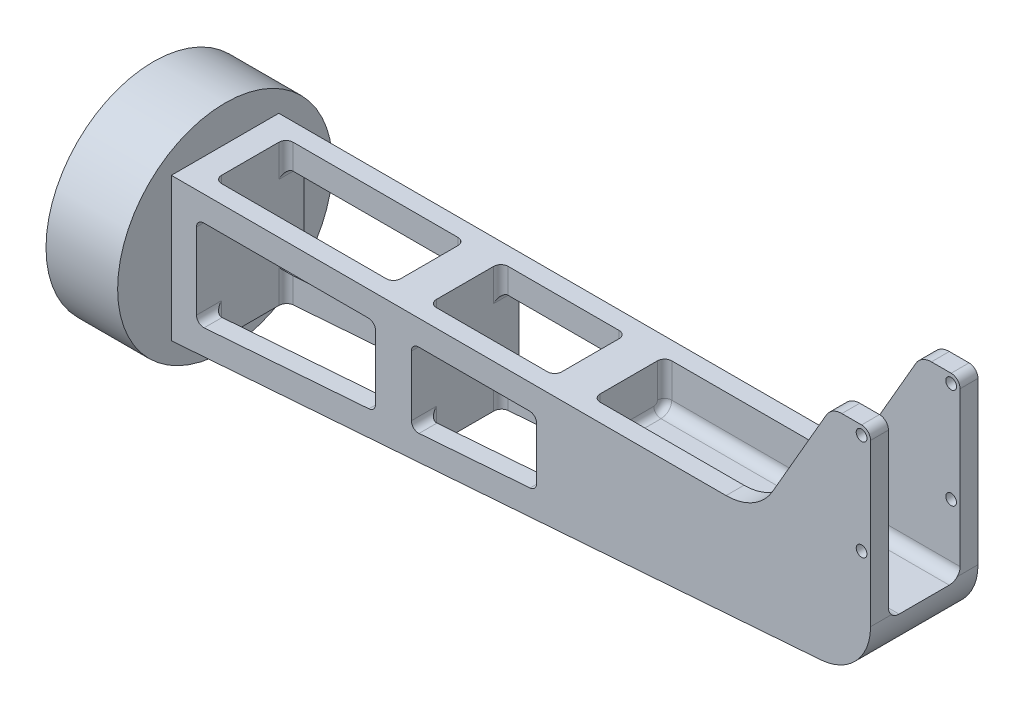
SolidWorks part; units mm, degrees
ref_plane "Front Plane" through (0, 0, 0) normal (0, 0, 1) x (1, 0, 0)
ref_plane "Top Plane" through (0, 0, 0) normal (0, 1, 0) x (1, 0, 0)
ref_plane "Right Plane" through (0, 0, 0) normal (1, 0, 0) x (0, 0, -1)
sketch "SideProfile" plane through (0, 0, 0) normal (0, 0, 1) x (1, 0, 0)
  line L0 (0, 0) -> (0, 28) construction
  line L1 (0, 28) -> (78.5, 28) construction
  line L2 (78.5, 28) -> (72.0655, 14.4502) construction
  line L3 (72.0655, 14.4502) -> (0, 0) construction
  line L4 (0, 0) -> (-27.9563, 16.574) construction
  line L5 (-27.9563, 16.574) -> (-60.4805, -10) construction
  line L6 (72.0655, 14.4502) -> (145.1629, -45.4258) construction
  line L7 (145.1629, -45.4258) -> (122.4038, 18.425) construction
  line L8 (75.2828, 21.2251) -> (98.855, 10.0312) construction
  line L9 (98.855, 10.0312) -> (122.4038, 18.425) construction
  line L10 (-192.7, -25.5) -> (0, -25.5) construction
  line L11 (-192.7, -25.5) -> (-192.7, -81.51) construction
  line L12 (-60.48, -18) -> (0, -18) construction
  line L14 (-212.7, 4.5) -> (-192.7, 4.5) construction
  line L15 (-212.7, 4.5) -> (-212.7, -55.5) construction
  line L16 (-212.7, -55.5) -> (-192.7, -55.5) construction
  line L17 (-192.7, 4.5) -> (-192.7, -55.5) construction
  circle A0 centre (0, 28) radius 2.5 construction
  circle A1 centre (0, 28) radius 1.5 construction
  point P22 (-192.7, -25.5)
  dimension "D18" = 5
  dimension "D19" = 3
  dimension "D1" = 28
  dimension "D2" = 78.5
  dimension "D3" = 15
  dimension "D4" = 73.5
  dimension "D5" = 138
  dimension "D6" = 32.5
  dimension "D7" = 42
  dimension "D8" = 10
  dimension "D9" = 94.49
  dimension "D10" = 103.92
  dimension "D11" = 31.06
  dimension "D12" = 25
  dimension "D13" = 25.5
  dimension "D14" = 192.7
  dimension "D15" = 56.01
  dimension "D16" = 8
  dimension "D17" = 60.48
  dimension "D20" = 60
  dimension "D21" = 20
sketch "TopProfile" plane through (0, 0, 0) normal (0, 1, 0) x (1, 0, 0)
  line L0 (0, -10) -> (0, 10) construction
  line L1 (0, -4) -> (0, 4) construction
  line L2 (0, -6) -> (0, 6) construction
  point P4 (0, 0)
  point P8 (0, 0)
  point P10 (0, 0)
  dimension "D1" = 20
  dimension "D2" = 4
  dimension "D3" = 2
sketch "Sketch2" plane through (0, 0, 0) normal (0, 0, 1) x (1, 0, 0)
  line L0 (2.5, -17.0414) -> (2.5, 28)
  line L4 (-192.7, -45.5) -> (-11.3862, -32)
  line L5 (-37.8316, -5.5) -> (-192.7, -5.5)
  line L6 (-192.7, -5.5) -> (-192.7, -45.5)
  line L7 (0, 30.5) -> (-5.5, 30.5)
  line L8 (-9.8301, 28) -> (-24.8412, 2)
  line L9 (-192.7, -25.5) -> (-192.7, -81.51) construction
  line L10 (-192.7, -25.5) -> (0, -25.5) construction
  circle A0 centre (0, 28) radius 1.5
  circle A1 centre (0, 0) radius 1.5
  arc A2 (2.5, 28) -> (0, 30.5) centre (0, 28) ccw
  arc A4 (2.5, -17.0414) -> (-11.3862, -32) centre (-12.5, -17.0414) cw
  arc A5 (-24.8412, 2) -> (-37.8316, -5.5) centre (-37.8316, 9.5) cw
  arc A6 (-5.5, 30.5) -> (-9.8301, 28) centre (-5.5, 25.5) ccw
  circle A7 centre (0, 28) radius 2.5 construction
  circle A8 centre (0, 28) radius 1.5 construction
  point P15 (2.5, -30.9661)
  point P19 (2.5, -30.9661)
  point P24 (-192.7, -25.5)
  dimension "D6" = 15
  dimension "D2" = 60
  dimension "D1" = 5
  dimension "D3" = 26.5
  dimension "D7" = 20
  dimension "D8" = 30
  dimension "D9" = 8
extrude "Boss-Extrude1" add sketch "Sketch2" along normal mid plane 30
sketch "Sketch3" plane through (0, 0, 0) normal (1, 0, 0) x (0, 0, -1)
  line L1 (-7, -18) -> (7, -18)
  line L2 (-10, -15) -> (-10, 30.5)
  line L3 (-10, 30.5) -> (10, 30.5)
  line L4 (10, -15) -> (10, 30.5)
  line L6 (-15, 30.5) -> (15, 30.5) construction
  line L7 (-10, 0) -> (10, 0) construction
  arc A0 (7, -18) -> (10, -15) centre (7, -15) ccw
  arc A1 (-7, -18) -> (-10, -15) centre (-7, -15) cw
  point P8 (0, 30.5)
  point P16 (-10, -18)
  dimension "D2" = 3
extrude "Cut-Extrude1" cut sketch "Sketch3" against normal blind 80 and the other way through all
ref_plane "Plane4" through (-192.7, 0, 0) normal (1, 0, 0) x (0, 0, -1)
sketch "Sketch4" plane through (-192.7, 0, 0) normal (1, 0, 0) x (0, 0, -1)
  line L0 (0, -25.5) -> (0, -81.51) construction
  circle A0 centre (0, -25.5) radius 30
extrude "Boss-Extrude2" add sketch "Sketch4" against normal up to vertex (20 mm away) up to point (-212.7, 4.5, 0)
fillet "Fillet1" radius 2 5 edges at (-80, -10.25, 10) (-80, -17.1213, 9.1213) (-80, -18, 0) (-80, -17.1213, -9.1213) (-80, -10.25, -10)
sketch "Sketch5" plane through (0, 0, 0) normal (0, 0, 1) x (1, 0, 0)
  line L0 (-185.7, -14.5) -> (-185.7, -35.805)
  line L1 (-183.5515, -37.7995) -> (-137.5515, -34.3745)
  line L2 (-135.7, -32.38) -> (-135.7, -14.5)
  line L3 (-137.7, -12.5) -> (-183.7, -12.5)
  line L4 (-125.7, -14.5) -> (-125.7, -31.3376)
  line L5 (-123.5515, -33.3321) -> (-92.5515, -31.0239)
  line L6 (-90.7, -29.0294) -> (-90.7, -14.5)
  line L7 (-92.7, -12.5) -> (-123.7, -12.5)
  line L8 (-192.7, -45.5) -> (-11.3862, -32) construction
  line L9 (-192.7, -55.5) -> (-192.7, 4.5) construction
  line L10 (-37.8316, -5.5) -> (-192.7, -5.5) construction
  arc A0 (-90.7, -14.5) -> (-92.7, -12.5) centre (-92.7, -14.5) ccw
  arc A1 (-92.5515, -31.0239) -> (-90.7, -29.0294) centre (-92.7, -29.0294) ccw
  arc A2 (-125.7, -31.3376) -> (-123.5515, -33.3321) centre (-123.7, -31.3376) ccw
  arc A3 (-125.7, -14.5) -> (-123.7, -12.5) centre (-123.7, -14.5) cw
  arc A4 (-135.7, -14.5) -> (-137.7, -12.5) centre (-137.7, -14.5) ccw
  arc A5 (-137.5515, -34.3745) -> (-135.7, -32.38) centre (-137.7, -32.38) ccw
  arc A6 (-185.7, -35.805) -> (-183.5515, -37.7995) centre (-183.7, -35.805) ccw
  arc A7 (-185.7, -14.5) -> (-183.7, -12.5) centre (-183.7, -14.5) cw
  dimension "D7" = 2
  dimension "D1" = 7
  dimension "D2" = 7
  dimension "D3" = 7
  dimension "D4" = 50
  dimension "D5" = 10
  dimension "D6" = 35
extrude "Cut-Extrude2" cut sketch "Sketch5" against normal through all both and the other way through all
sketch "Sketch6" plane through (0, 0, 0) normal (0, 1, 0) x (1, 0, 0)
  line L0 (-37.8316, 15) -> (-192.7, 15) construction
  line L1 (-183.7, 10) -> (-137.7, 10)
  line L2 (-185.7, 8) -> (-185.7, -8)
  line L3 (-183.7, -10) -> (-137.7, -10)
  line L4 (-135.7, 8) -> (-135.7, -8)
  line L5 (-123.7, 10) -> (-92.7, 10)
  line L6 (-125.7, 8) -> (-125.7, -8)
  line L7 (-123.7, -10) -> (-92.7, -10)
  line L8 (-90.7, 8) -> (-90.7, -8)
  arc A0 (-92.7, 10) -> (-90.7, 8) centre (-92.7, 8) cw
  arc A1 (-92.7, -10) -> (-90.7, -8) centre (-92.7, -8) ccw
  arc A2 (-125.7, -8) -> (-123.7, -10) centre (-123.7, -8) ccw
  arc A3 (-123.7, 10) -> (-125.7, 8) centre (-123.7, 8) ccw
  arc A4 (-137.7, 10) -> (-135.7, 8) centre (-137.7, 8) cw
  arc A5 (-137.7, -10) -> (-135.7, -8) centre (-137.7, -8) ccw
  arc A6 (-185.7, -8) -> (-183.7, -10) centre (-183.7, -8) ccw
  arc A7 (-183.7, 10) -> (-185.7, 8) centre (-183.7, 8) ccw
  point P8 (-135.7, 0)
  point P9 (-90.7, 0)
  dimension "D2" = 2
  dimension "D1" = 5
extrude "Cut-Extrude3" cut sketch "Sketch6" against normal through all both and the other way through all
